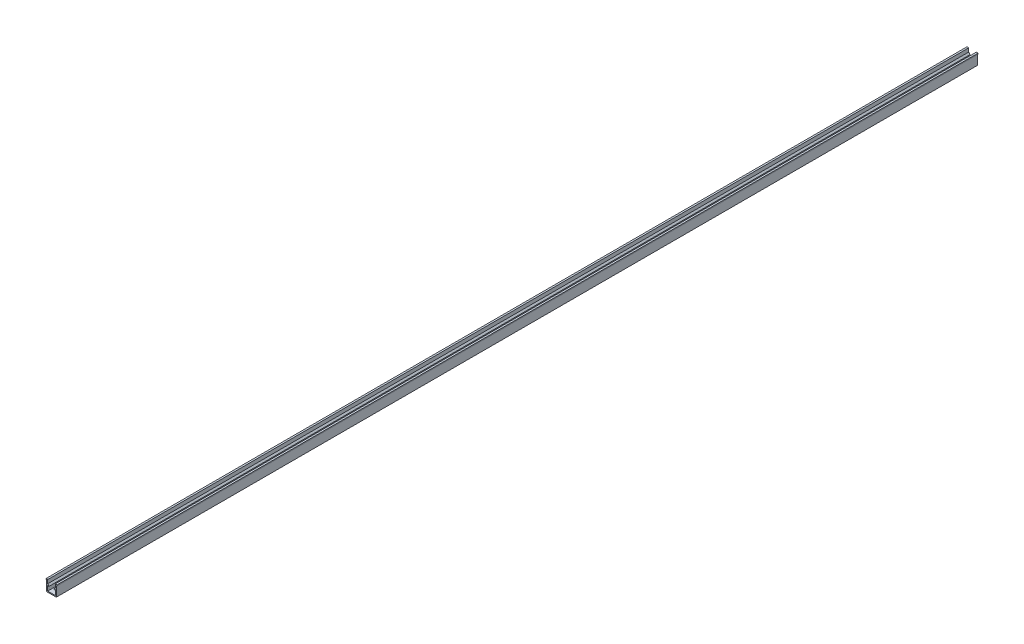
SolidWorks part; units mm, degrees
material "Пластик"
ref_plane "Спереди" through (0, 0, 0) normal (0, 0, 1) x (1, 0, 0)
ref_plane "Сверху" through (0, 0, 0) normal (0, 1, 0) x (1, 0, 0)
ref_plane "Справа" through (0, 0, 0) normal (1, 0, 0) x (0, 0, -1)
sketch "Эскиз1" plane through (0, 0, 0) normal (0, 0, 1) x (1, 0, 0)
  line L0 (5.2, 0) -> (-5.2, 0)
  line L1 (-5.2, 0) -> (-5.2, 11)
  line L2 (-5.2, 11) -> (-6, 11)
  line L3 (-6, 11) -> (-6, 12)
  line L4 (-6, 12) -> (-4.1, 12)
  line L5 (-4.1, 12) -> (-4.1, 8)
  line L6 (-4.1, 8) -> (-2.5444, 6.4444)
  line L7 (-2.5444, 6.4444) -> (-3.2515, 5.7373)
  line L8 (-3.2515, 5.7373) -> (-4.1, 6.5858)
  line L9 (-4.1, 6.5858) -> (-4.1, 1.1)
  line L10 (-4.1, 1.1) -> (4.1, 1.1)
  line L11 (0, 1.1) -> (0, 0) construction
  line L12 (4.1, 6.5858) -> (4.1, 1.1)
  line L13 (3.2515, 5.7373) -> (4.1, 6.5858)
  line L14 (2.5444, 6.4444) -> (3.2515, 5.7373)
  line L15 (4.1, 8) -> (2.5444, 6.4444)
  line L16 (4.1, 12) -> (4.1, 8)
  line L17 (6, 12) -> (4.1, 12)
  line L18 (6, 11) -> (6, 12)
  line L19 (5.2, 11) -> (6, 11)
  line L20 (5.2, 0) -> (5.2, 11)
  line L21 (-5.2, 5.5) -> (-4.1, 5.5) construction
  dimension "D1" = 10.4
  dimension "D2" = 12
  dimension "D3" = 8.2
  dimension "D4" = 12
  dimension "D5" = 1
  dimension "D6" = 135
  dimension "D7" = 2.2
  dimension "D8" = 1
  dimension "D9" = 4
extrude "Бобышка-Вытянуть1" add sketch "Эскиз1" along normal blind 1000
